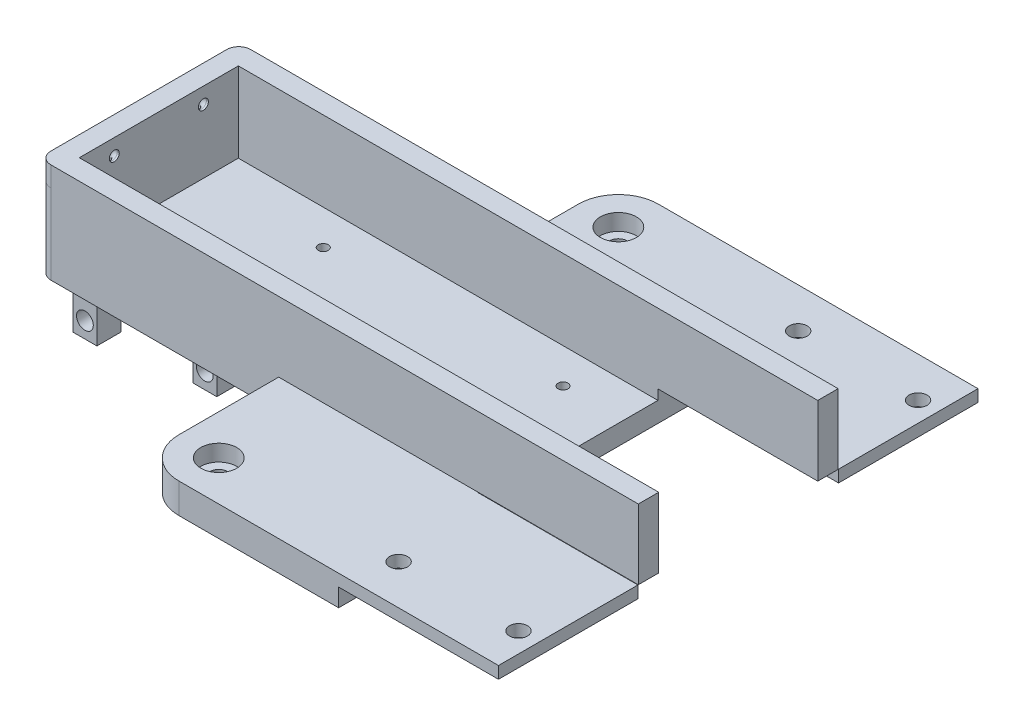
SolidWorks part; units mm, degrees
ref_plane "정면" through (0, 0, 0) normal (0, 0, 1) x (1, 0, 0)
ref_plane "윗면" through (0, 0, 0) normal (0, 1, 0) x (1, 0, 0)
ref_plane "우측면" through (0, 0, 0) normal (1, 0, 0) x (0, 0, -1)
sketch "스케치1" plane through (0, 0, 0) normal (0, 1, 0) x (1, 0, 0)
  line L1 (-150, 25) -> (150, 25)
  line L2 (-150, 25) -> (-150, -25)
  line L3 (-150, -25) -> (150, -25)
  line L4 (150, 25) -> (150, -25)
  line L5 (-150, 25) -> (150, -25) construction
  line L6 (-150, -25) -> (150, 25) construction
  point P0 (0, 0)
  dimension "D1" = 300
  dimension "D2" = 50
extrude "보스-돌출1" add sketch "스케치1" along normal mid plane 20
sketch "스케치2" plane through (0, 10, 0) normal (0, 1, 0) x (1, 0, 0)
  line L0 (-150, 25) -> (-150, -25) construction
  line L1 (-150, 16.2) -> (150, 16.2)
  line L2 (-150, 16.2) -> (-150, 6.1)
  line L3 (-150, 6.1) -> (150, 6.1)
  line L4 (150, 16.2) -> (150, 6.1)
  line L5 (150, -25) -> (150, 25) construction
  line L6 (150, 25) -> (-150, 25) construction
  line L8 (-150, 4.6) -> (150, 4.6)
  line L9 (-150, 4.6) -> (-150, -4.6)
  line L10 (-150, -4.6) -> (150, -4.6)
  line L11 (150, 4.6) -> (150, -4.6)
  line L12 (-150, -6.1) -> (150, -6.1)
  line L13 (-150, -6.1) -> (-150, -16.2)
  line L14 (-150, -16.2) -> (150, -16.2)
  line L15 (150, -6.1) -> (150, -16.2)
  dimension "D1" = 10.1
  dimension "D2" = 8.8
  dimension "D3" = 1.5
  dimension "D4" = 9.2
  dimension "D5" = 1.5
  dimension "D6" = 10.1
extrude "컷-돌출1" cut sketch "스케치2" against normal blind 5
sketch "스케치9" plane through (0, 5, 0) normal (0, 1, 0) x (1, 0, 0)
  line L0 (150, 16.2) -> (-150, 16.2) construction
  line L1 (-142.5, 14.57) -> (142.5, 14.57)
  line L3 (-142.5, 10.17) -> (142.5, 10.17)
  line L5 (-142.5, 14.57) -> (142.5, 10.17) construction
  line L6 (-142.5, 10.17) -> (142.5, 14.57) construction
  line L7 (0, 0) -> (18.1347, 0) construction
  line L8 (0, 12.37) -> (0, 28.3671) construction
  line L9 (0, -12.37) -> (0, -28.3671) construction
  line L10 (-142.5, -10.17) -> (142.5, -14.57) construction
  line L11 (-142.5, -14.57) -> (142.5, -10.17) construction
  line L12 (-142.5, -10.17) -> (142.5, -10.17)
  line L13 (-142.5, -14.57) -> (142.5, -14.57)
  arc A0 (142.5, 14.57) -> (142.5, 10.17) centre (142.5, 12.37) cw
  arc A2 (-142.5, 14.57) -> (-142.5, 10.17) centre (-142.5, 12.37) ccw
  arc A3 (-142.5, -14.57) -> (-142.5, -10.17) centre (-142.5, -12.37) cw
  arc A4 (142.5, -14.57) -> (142.5, -10.17) centre (142.5, -12.37) ccw
  point P0 (0, 12.37)
  point P22 (0, -12.37)
  dimension "D4" = 2.2
  dimension "D1" = 285
  dimension "D2" = 4.4
  dimension "D3" = 1.63
extrude "컷-돌출3" [suppressed] cut sketch "스케치9" against normal through all
fillet "필렛1" radius 3 4 edges at (150, 0, 25) (150, 0, -25) (-150, 0, -25) (-150, 0, 25)
sketch "스케치10" plane through (-150, 0, 0) normal (-1, 0, 0) x (0, 0, 1)
  line L0 (0, 0) -> (0, 7.0136) construction
  line L10 (-19.9, -5) -> (19.9, -5)
  line L11 (-19.9, -5) -> (-19.9, 10)
  line L16 (11.15, 5) -> (11.15, 5.9581) construction
  line L22 (-11.15, 5) -> (-11.15, 5.9581) construction
  line L23 (-16.2, 5) -> (-6.1, 5) construction
  line L24 (-19.9, 10) -> (19.9, 10)
  line L36 (19.9, -5) -> (19.9, 10)
  line L38 (-22, -10) -> (22, -10) construction
  line L39 (-22, 10) -> (-16.2, 10) construction
  dimension "D1" = 39.8
  dimension "D2" = 5
extrude "컷-돌출4" cut sketch "스케치10" against normal blind 145 from offset 5 offset against normal yes
sketch "스케치12" plane through (0, 0, 25) normal (0, 0, 1) x (1, 0, 0)
  line L0 (-40, -10) -> (-40, -2.5)
  line L1 (0, 10) -> (150, 10)
  line L3 (-40, -10) -> (150, -10)
  line L4 (150, 10) -> (150, -10)
  line L5 (-40, -2.5) -> (0, -2.5)
  line L9 (-147, 10) -> (147, 10) construction
  line L12 (0, -2.5) -> (0, 10)
  dimension "D1" = 190
  dimension "D2" = 150
  dimension "D3" = 7.5
extrude "컷-돌출6" cut sketch "스케치12" against normal through all
sketch "스케치13" plane through (0, -10, 0) normal (0, -1, 0) x (-1, 0, 0)
  line L0 (147, -25) -> (40, -25) construction
  line L1 (90, -60) -> (40, -60)
  line L2 (90, -60) -> (90, -25)
  line L3 (90, -25) -> (40, -25)
  line L4 (40, -60) -> (40, -25)
  line L5 (90, -60) -> (40, -25) construction
  line L6 (90, -25) -> (40, -60) construction
  line L7 (40, 25) -> (40, -25) construction
  line L8 (0, 0) -> (20.621, 0) construction
  line L9 (0, 6.1) -> (0, -6.1) construction
  line L10 (90, 25) -> (40, 60) construction
  line L11 (90, 60) -> (40, 25) construction
  line L12 (40, 60) -> (40, 25)
  line L13 (90, 25) -> (40, 25)
  line L14 (90, 60) -> (90, 25)
  line L15 (90, 60) -> (40, 60)
  point P0 (65, -42.5)
  point P17 (65, 42.5)
  dimension "D1" = 50
  dimension "D2" = 35
extrude "보스-돌출2" add sketch "스케치13" against normal blind 7.5
hole_wizard "M4 남비 머리 나사용 카운터보어1" positions "스케치14" profile "스케치15" counterbore size "M4" standard "ISO" end condition through all
sketch "스케치14" plane through (0, -2.5, 0) normal (0, 1, 0) x (1, 0, 0)
  line L0 (0, 0) -> (-21.6162, 0) construction
  line L1 (0, 4.6) -> (0, -4.6) construction
  line L3 (-90, 25) -> (-90, 60) construction
  line L4 (-90, 60) -> (-40, 60) construction
  point P0 (-80, 50)
  point P8 (-80, -50)
  dimension "D1" = 10
  dimension "D2" = 10
sketch "스케치15" plane through (-80, -2.5, -50) normal (1, 0, 0) x (0, 0, 1)
  line L0 (0, 0) -> (0, 7.5)
  line L1 (0, 7.5) -> (2.25, 7.5)
  line L3 (2.25, 7.5) -> (2.25, 4.1)
  line L4 (2.25, 4.1) -> (4.5, 4.1)
  line L5 (4.5, 4.1) -> (4.5, 0)
  line L7 (4.5, 0) -> (0, 0)
  line L11 (0, -6.35) -> (0, 107.95) construction
  dimension "관통 구멍 지름" = 4.5
  dimension "관통 구멍 깊이" = 7.5
  dimension "카운터보어 지름" = 9
  dimension "카운터보어 깊이" = 4.1
sketch "스케치16" plane through (0, -10, 0) normal (0, -1, 0) x (-1, 0, 0)
  line L0 (150, 22) -> (150, -22) construction
  line L1 (115, -21.5) -> (109, -21.5)
  line L2 (115, -21.5) -> (115, -15.5)
  line L3 (115, -15.5) -> (109, -15.5)
  line L4 (109, -21.5) -> (109, -15.5)
  line L5 (115, -21.5) -> (109, -15.5) construction
  line L6 (115, -15.5) -> (109, -21.5) construction
  line L7 (115, -8) -> (109, -8)
  line L8 (115, -8) -> (115, -2)
  line L9 (115, -2) -> (109, -2)
  line L10 (109, -8) -> (109, -2)
  line L11 (115, -8) -> (109, -2) construction
  line L12 (115, -2) -> (109, -8) construction
  line L13 (90, 25) -> (147, 25) construction
  line L14 (150, 0) -> (130.217, 0) construction
  line L15 (115, 2) -> (109, 8) construction
  line L16 (115, 8) -> (109, 2) construction
  line L17 (115, 15.5) -> (109, 21.5) construction
  line L18 (115, 21.5) -> (109, 15.5) construction
  line L19 (109, 8) -> (109, 2)
  line L20 (115, 2) -> (109, 2)
  line L21 (115, 8) -> (115, 2)
  line L22 (115, 8) -> (109, 8)
  line L23 (109, 21.5) -> (109, 15.5)
  line L24 (115, 15.5) -> (109, 15.5)
  line L25 (115, 21.5) -> (115, 15.5)
  line L26 (115, 21.5) -> (109, 21.5)
  point P0 (112, -18.5)
  point P5 (112, -5)
  point P25 (112, 5)
  point P26 (112, 18.5)
  dimension "D1" = 6
  dimension "D2" = 6
  dimension "D3" = 35
  dimension "D4" = 7.5
  dimension "D5" = 27
extrude "보스-돌출3" add sketch "스케치16" along normal blind 8
sketch "스케치17" plane through (0, 0, 21.5) normal (0, 0, 1) x (1, 0, 0)
  line L0 (-115, -18) -> (-115, -10) construction
  line L1 (-109, -10) -> (-115, -10) construction
  circle A0 centre (-112, -14) radius 2.1
  dimension "D1" = 3
  dimension "D2" = 4
  dimension "D3" = 4.2
extrude "컷-돌출7" cut sketch "스케치17" against normal through all
sketch "스케치18" plane through (0, -10, 0) normal (0, -1, 0) x (1, 0, 0)
  line L2 (-90, 60) -> (-90, 25) construction
  line L3 (-40, 60) -> (-90, 60) construction
  circle A1 centre (-82, 38) radius 2
  dimension "D1" = 4
  dimension "D2" = 8
  dimension "D3" = 22
extrude "컷-돌출8" [suppressed] cut sketch "스케치18" against normal blind 4
sketch "스케치19" plane through (0, -10, 0) normal (0, -1, 0) x (1, 0, 0)
  line L0 (-150, -22) -> (-150, 22) construction
  line L1 (-145, 21.5) -> (-139, 21.5)
  line L2 (-145, 21.5) -> (-145, 15.5)
  line L3 (-145, 15.5) -> (-139, 15.5)
  line L4 (-139, 21.5) -> (-139, 15.5)
  line L5 (-145, 21.5) -> (-139, 15.5) construction
  line L6 (-145, 15.5) -> (-139, 21.5) construction
  line L7 (-145, 7.5) -> (-139, 7.5)
  line L8 (-145, 7.5) -> (-145, 1.5)
  line L9 (-145, 1.5) -> (-139, 1.5)
  line L10 (-139, 7.5) -> (-139, 1.5)
  line L11 (-145, 7.5) -> (-139, 1.5) construction
  line L12 (-145, 1.5) -> (-139, 7.5) construction
  line L13 (-115, 21.5) -> (-115, 15.5) construction
  line L14 (-109, 21.5) -> (-115, 21.5) construction
  line L15 (-150, 0) -> (-132.5581, 0) construction
  line L16 (-147, 25) -> (-90, 25) construction
  line L17 (-145, -1.5) -> (-139, -7.5) construction
  line L18 (-145, -7.5) -> (-139, -1.5) construction
  line L19 (-145, -15.5) -> (-139, -21.5) construction
  line L20 (-145, -21.5) -> (-139, -15.5) construction
  line L21 (-139, -7.5) -> (-139, -1.5)
  line L22 (-145, -1.5) -> (-139, -1.5)
  line L23 (-145, -7.5) -> (-145, -1.5)
  line L24 (-145, -7.5) -> (-139, -7.5)
  line L25 (-139, -21.5) -> (-139, -15.5)
  line L26 (-145, -15.5) -> (-139, -15.5)
  line L27 (-145, -21.5) -> (-145, -15.5)
  line L28 (-145, -21.5) -> (-139, -21.5)
  point P0 (-142, 18.5)
  point P5 (-142, 4.5)
  point P29 (-142, -4.5)
  point P30 (-142, -18.5)
  dimension "D1" = 5
  dimension "D2" = 3.5
  dimension "D3" = 8
extrude "보스-돌출4" add sketch "스케치19" along normal blind 12
sketch "스케치20" plane through (0, 0, 21.5) normal (0, 0, 1) x (1, 0, 0)
  line L0 (-145, -22) -> (-145, -10) construction
  line L1 (-139, -22) -> (-145, -22) construction
  circle A0 centre (-142, -18) radius 2.1
  dimension "D1" = 3
  dimension "D2" = 4
  dimension "D3" = 4.2
extrude "컷-돌출9" cut sketch "스케치20" against normal through all
ref_plane "평면1" through (0, 0, 11.15) normal (0, 0, -1) x (-1, 0, 0)
sketch "스케치23" plane through (-40, 0, 0) normal (1, 0, 0) x (0, 0, -1)
  line L0 (-25, 10) -> (-25, -2.5) construction
  line L1 (-60, -2.5) -> (-25.1, -2.5)
  line L2 (-60, -2.5) -> (-60, -5.5)
  line L3 (-60, -5.5) -> (-25.1, -5.5)
  line L4 (-25.1, -2.5) -> (-25.1, -5.5)
  line L9 (60, -2.5) -> (25, -2.5) construction
  line L11 (60, -2.5) -> (60, -10) construction
  line L12 (25.1, -2.5) -> (60, -2.5)
  line L13 (25.1, -2.5) -> (25.1, -5.5)
  line L14 (25.1, -5.5) -> (60, -5.5)
  line L15 (60, -2.5) -> (60, -5.5)
  line L16 (25, 10) -> (25, -2.5) construction
  dimension "D1" = 3
  dimension "D2" = 0.1
  dimension "D3" = 0.1
extrude "보스-돌출9" add sketch "스케치23" along normal up to surface (40 mm away) up to face at (0, 3.75, 22.45)
hole_wizard "M4 여유 구멍1" positions "스케치25" profile "스케치26" hole size "M4" standard "ISO" end condition through all
sketch "스케치25" plane through (0, -2.5, 0) normal (0, 1, 0) x (1, 0, 0)
  line L1 (0, 25.1) -> (0, 60) construction
  line L2 (-90, 60) -> (0, 60) construction
  line L3 (0, 0) -> (-24.5664, 0) construction
  point P0 (-35, 50)
  point P3 (-5, 50)
  point P6 (-5, -50)
  point P9 (-35, -50)
  point P27 (0, 0)
  point P28 (0, 0)
  point P29 (0, 0)
  dimension "D1" = 5
  dimension "D2" = 30
  dimension "D3" = 10
sketch "스케치26" plane through (-35, -2.5, -50) normal (1, 0, 0) x (0, 0, 1)
  line L0 (0, 0) -> (0, 19.5)
  line L1 (0, 19.5) -> (2.25, 19.5)
  line L2 (2.25, 19.5) -> (2.25, 0)
  line L5 (2.25, 0) -> (0, 0)
  line L11 (0, -6.35) -> (0, 107.95) construction
  dimension "관통 구멍 지름" = 4.5
  dimension "관통 구멍 깊이" = 19.5
fillet "필렛2" radius 0.5 1 edges at (-109, -14, 15.5)
sketch "스케치27" plane through (0, 5, 0) normal (0, 1, 0) x (1, 0, 0)
  line L0 (-145, -6.1) -> (-145, -16.2) construction
  line L1 (-150, 16.2) -> (-145, 16.2)
  line L2 (-150, 16.2) -> (-150, -16.2)
  line L3 (-150, -16.2) -> (-145, -16.2)
  line L4 (-145, 16.2) -> (-145, -16.2)
  line L5 (-150, -16.2) -> (-145, -16.2) construction
extrude "보스-돌출10" add sketch "스케치27" along normal up to surface (5 mm away) up to face at (-105.3745, 10, -20.6888)
sketch "스케치28" plane through (0, -10, 0) normal (0, -1, 0) x (-1, 0, 0)
  line L1 (42, 15) -> (48, 15)
  line L2 (42, 15) -> (42, 9)
  line L3 (42, 9) -> (48, 9)
  line L4 (48, 15) -> (48, 9)
  line L5 (42, 15) -> (48, 9) construction
  line L6 (42, 9) -> (48, 15) construction
  line L10 (90, 60) -> (40, 60) construction
  line L11 (40, 60) -> (40, -60) construction
  point P0 (45, 12)
  dimension "D1" = 6
  dimension "D2" = 6
  dimension "D3" = 5
  dimension "D4" = 48
extrude "보스-돌출11" [suppressed] add sketch "스케치28" along normal blind 8
sketch "스케치29" [suppressed] plane through (-48, 0, 0) normal (-1, 0, 0) x (0, 0, 1)
  line L0 (0, -18) -> (0, -10) construction
  line L1 (6, -18) -> (0, -18) construction
  circle A0 centre (3, -14) radius 2.1
  dimension "D2" = 4
  dimension "D3" = 4.2
  dimension "D1" = 3
extrude "컷-돌출10" [suppressed] cut sketch "스케치29" against normal up to next
hole_wizard "M3 나사 구멍1" positions "스케치32" profile "스케치33" tap size "M3" standard "ISO" end condition up to next
sketch "스케치32" plane through (0, -5, 0) normal (0, 1, 0) x (1, 0, 0)
  point P0 (-115, 11.15)
  point P2 (-115, -11.15)
  point P4 (-55, 11.15)
  point P6 (-55, -11.15)
sketch "스케치33" plane through (-115, -5, -11.15) normal (1, 0, 0) x (0, 0, 1)
  line L0 (0, 0) -> (0, 5)
  line L1 (0, 5) -> (1.25, 5)
  line L2 (1.25, 5) -> (1.25, 0)
  line L5 (1.25, 0) -> (0, 0)
  line L11 (0, -6.35) -> (0, 107.95) construction
  dimension "관통 탭 드릴 지름" = 2.5
  dimension "관통 탭 드릴 깊이" = 5
cosmetic thread "구멍 나사산1" parameters "D2"=3
cosmetic thread "구멍 나사산2" parameters "D2"=3
cosmetic thread "구멍 나사산3" parameters "D2"=3
cosmetic thread "구멍 나사산4" parameters "D2"=3
sketch "스케치34" plane through (0, 10, 0) normal (0, 1, 0) x (1, 0, 0)
  line L0 (-147, -25) -> (0, -25) construction
  line L2 (-150, 25) -> (-150, -25)
  line L4 (-145, 19.9) -> (-145, -19.9)
  line L5 (-40, 25) -> (-90, 25) construction
  line L8 (-145, 19.9) -> (-145, -19.9) construction
  line L9 (-150, 22) -> (-150, -22) construction
  line L12 (-150, 25) -> (0, 25)
  line L14 (-145, 19.9) -> (0, 19.9)
  line L15 (0, 25) -> (0, 19.9)
  line L16 (-150, -25) -> (0, -25)
  line L18 (-145, -19.9) -> (0, -19.9)
  line L19 (0, -25) -> (0, -19.9)
  point P0 (-147.5, 0)
extrude "보스-돌출12" add sketch "스케치34" along normal blind 5
fillet "필렛3" radius 3 2 edges at (-150, 12.5, 25) (-150, 12.5, -25)
sketch "스케치21" plane through (0, -10, 0) normal (0, -1, 0) x (-1, 0, 0)
  line L2 (150, 22) -> (150, -22) construction
  line L3 (147, -25) -> (90, -25) construction
  line L4 (90, 25) -> (147, 25) construction
  circle A0 centre (147.5, -11.15) radius 1.25
  circle A1 centre (147.5, 11.15) radius 1.25
  dimension "D1" = 2.5
  dimension "D2" = 2.5
  dimension "D3" = 13.85
  dimension "D5" = 13.85
  dimension "D6" = 2.5
  dimension "D4" = 2.5
sketch "스케치22" plane through (0, 0, 11.15) normal (0, 0, -1) x (-1, 0, 0)
  line L0 (147.5, -10) -> (147.5, 9)
  line L1 (145.5, 11) -> (144.5, 11)
  line L2 (90, -10) -> (147, -10) construction
  line L3 (150, 10) -> (150, -10) construction
  arc A0 (147.5, 9) -> (145.5, 11) centre (145.5, 9) ccw
  point P10 (147.5, 11)
  dimension "D4" = 2
  dimension "D1" = 21
  dimension "D2" = 3
  dimension "D3" = 2.5
sweep "컷-스윕1" cut profiles "스케치21" path "스케치22"
fillet "필렛4" radius 10 2 edges at (-90, -6.25, -60) (-90, -6.25, 60)
